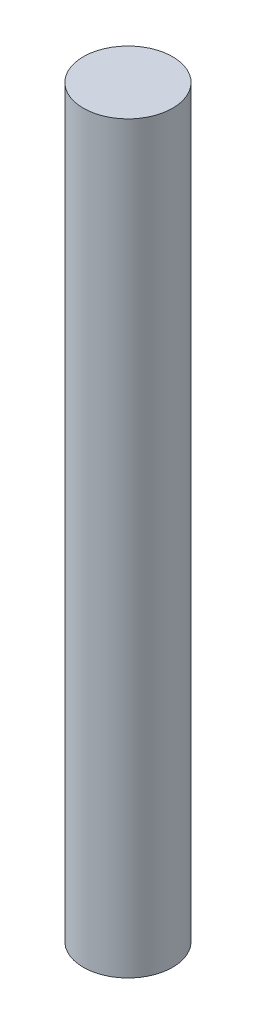
SolidWorks part; units mm, degrees
ref_plane "前基準面" through (0, 0, 0) normal (0, 0, 1) x (1, 0, 0)
ref_plane "上基準面" through (0, 0, 0) normal (0, 1, 0) x (1, 0, 0)
ref_plane "右基準面" through (0, 0, 0) normal (1, 0, 0) x (0, 0, -1)
sketch "草圖1" plane through (0, 0, 0) normal (0, 1, 0) x (1, 0, 0)
  circle A0 centre (0, 0) radius 7.5
  dimension "D1" = 15
extrude "填料-伸長1" add sketch "草圖1" along normal mid plane 125
